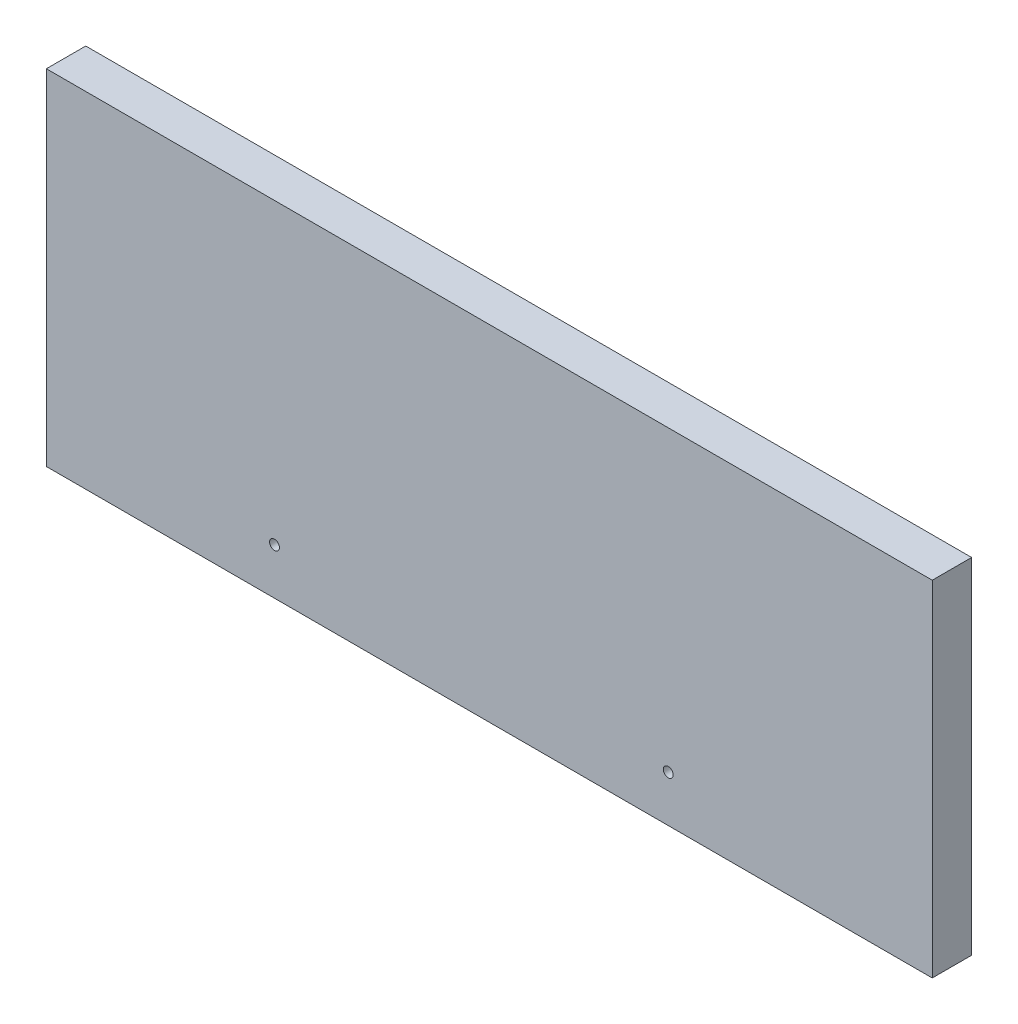
SolidWorks part; units mm, degrees
ref_plane "前视基准面" through (0, 0, 0) normal (0, 0, 1) x (1, 0, 0)
ref_plane "上视基准面" through (0, 0, 0) normal (0, 1, 0) x (1, 0, 0)
ref_plane "右视基准面" through (0, 0, 0) normal (1, 0, 0) x (0, 0, -1)
sketch "草图1" plane through (0, 0, 0) normal (0, 0, 1) x (1, 0, 0)
  line L1 (-225, -87.5) -> (225, -87.5)
  line L2 (-225, -87.5) -> (-225, 87.5)
  line L3 (-225, 87.5) -> (225, 87.5)
  line L4 (225, -87.5) -> (225, 87.5)
  line L5 (-225, -87.5) -> (225, 87.5) construction
  line L6 (-225, 87.5) -> (225, -87.5) construction
  point P0 (0, 0)
  dimension "D1" = 175
  dimension "D2" = 450
extrude "凸台-拉伸1" add sketch "草图1" along normal blind 20
sketch "草图2" plane through (0, 0, 20) normal (0, 0, 1) x (1, 0, 0)
  line L0 (-225, -87.5) -> (225, -87.5) construction
  line L1 (-225, 87.5) -> (-225, -87.5) construction
  circle A0 centre (-109.12, -64) radius 2.5
  circle A3 centre (90.88, -64) radius 2.5
  dimension "D1" = 5
  dimension "D2" = 115.88
  dimension "D3" = 23.5
  dimension "D4" = 200
extrude "切除-拉伸1" cut sketch "草图2" against normal through all contours A0 | A3
